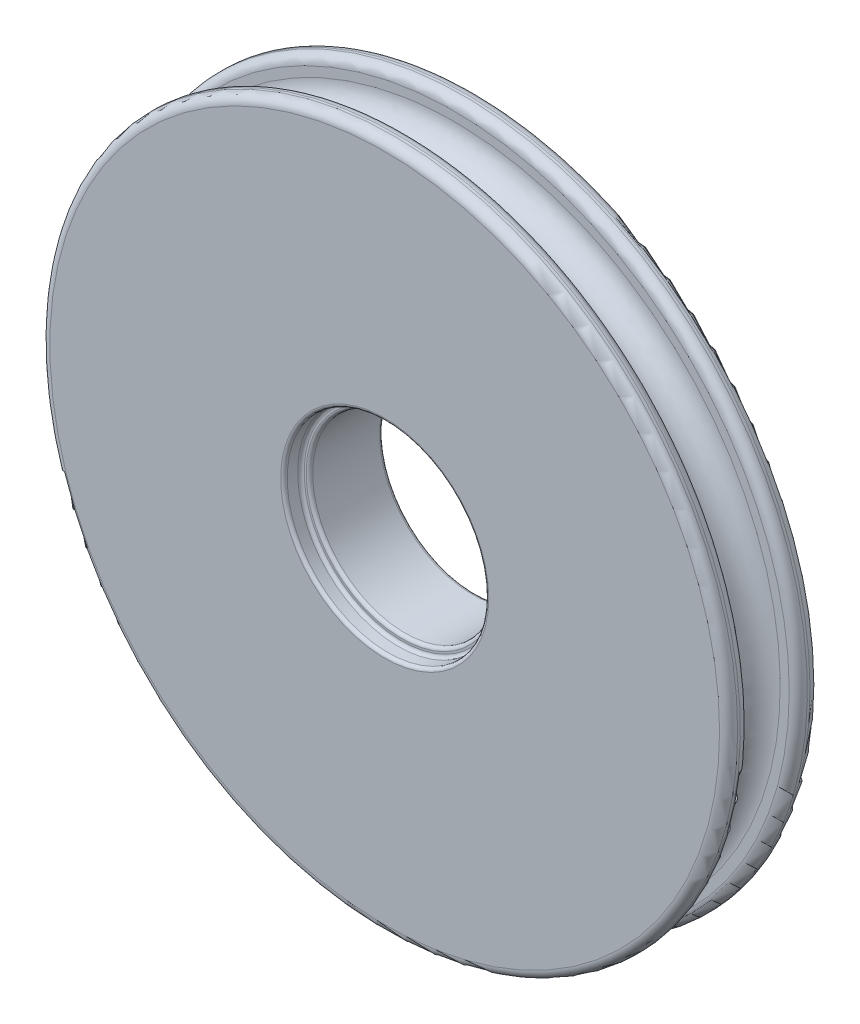
SolidWorks part; units mm, degrees
ref_plane "Front Plane" through (0, 0, 0) normal (0, 0, 1) x (1, 0, 0)
ref_plane "Top Plane" through (0, 0, 0) normal (0, 1, 0) x (1, 0, 0)
ref_plane "Right Plane" through (0, 0, 0) normal (1, 0, 0) x (0, 0, -1)
sketch "Sketch1" plane through (0, 0, 0) normal (0, 0, 1) x (1, 0, 0)
  circle A0 centre (0, 0) radius 24.13
  dimension "D1" = 48.26
extrude "Boss-Extrude1" add sketch "Sketch1" along normal mid plane 6.35
ref_plane "Plane1" through (0, 0, 0) normal (0, 0, -1) x (-1, 0, 0)
sketch "Sketch6" plane through (0, 0, 0) normal (0, 0, -1) x (-1, 0, 0)
  circle A0 centre (0, 0) radius 22.86
  dimension "D1" = 45.72
sketch3d "3DSketch1"
  line L0 (-4.6459, -22.3829, 0) -> (-4.6459, -22.3829, -1.7145) construction
  line L1 (-4.6459, -22.3829, -1.7145) -> (-4.6459, -25.6945, -1.7145)
  line L2 (-4.6459, -25.6945, -1.7145) -> (-4.6459, -25.6945, 1.7145)
  line L3 (-4.6459, -25.6945, 1.7145) -> (-4.6459, -22.3829, 1.7145)
  line L4 (-4.6459, -22.3829, 1.7145) -> (-4.6459, -22.3829, 0) construction
  circle A0 centre (-4.6459, -22.3829, 0) radius 1.7145 construction
  circle A1 centre (0, 0, 0) radius 22.86 construction
  arc A2 (-4.6459, -22.3829, 1.7145) -> (-4.6459, -22.3829, -1.7145) centre (-4.6459, -22.3829, 0) cw
  point P2 (-2.9314, -22.3829, 0)
  point P5 (0, 0, -22.86)
  point P11 (-6.3604, -22.3829, 0)
  dimension "D1" = 3.429
sweep "Cut-Sweep1" cut profiles "3DSketch1" path "Sketch6"
sketch "Sketch3" plane through (0, 0, 0) normal (0, 0, 1) x (1, 0, 0)
  circle A0 centre (0, 0) radius 4.7625
  dimension "D1" = 9.525
extrude "Cut-Extrude1" cut sketch "Sketch3" against normal mid plane 3.175
sketch "Sketch4" plane through (0, 0, 3.175) normal (0, 0, 1) x (1, 0, 0)
  circle A0 centre (0, 0) radius 6.477
  dimension "D1" = 12.954
extrude "Cut-Extrude2" cut sketch "Sketch4" against normal through all
sketch "Sketch5" plane through (0, 0, 3.175) normal (0, 0, 1) x (1, 0, 0)
  circle A0 centre (0, 0) radius 7.0723
  dimension "D1" = 14.1446
extrude "Cut-Extrude3" cut sketch "Sketch5" against normal blind 1.1906
fillet "Fillet2" radius 0.2286 4 edges at (6.477, 0, -3.175) (6.477, 0, 1.9844) (7.0723, 0, 1.9844) (7.0723, 0, 3.175)
fillet "Fillet3" radius 0.635 4 edges at (24.13, 0, -3.175) (-24.13, 0, -1.7145) (24.13, 0, 3.175) (24.13, 0, 1.7145)
